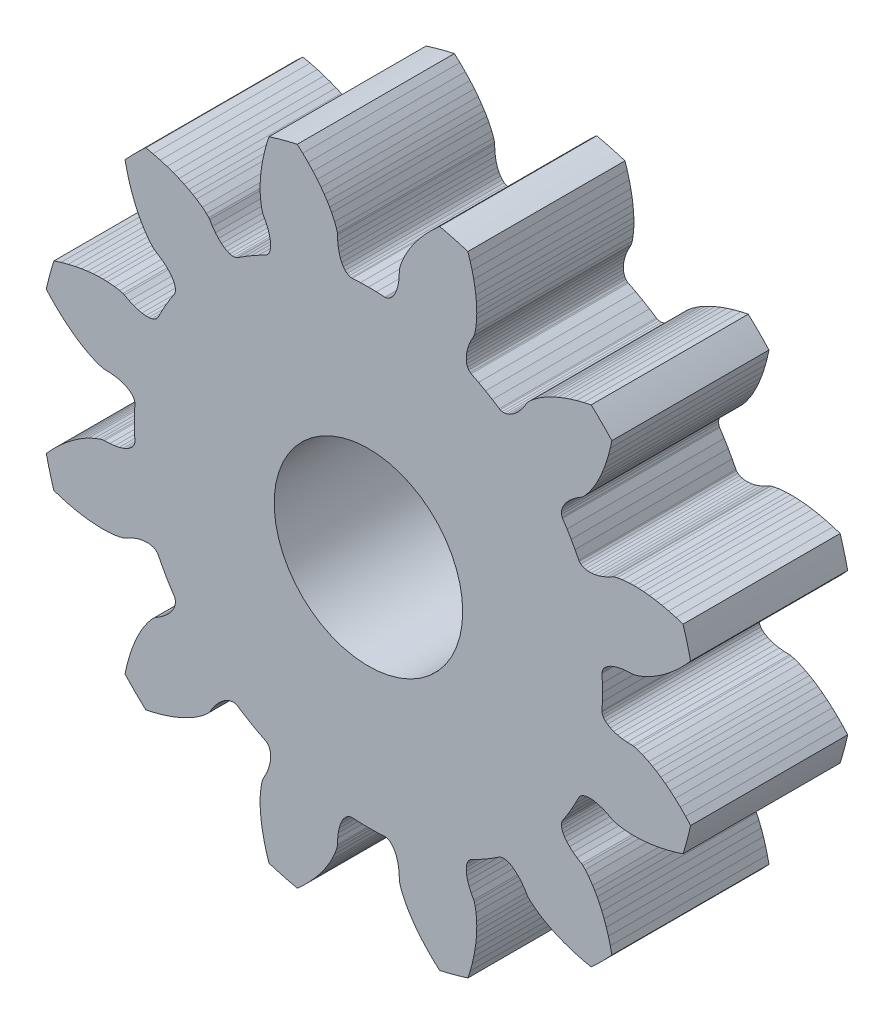
SolidWorks part; units mm, degrees
ref_plane "Płaszczyzna przednia" through (0, 0, 0) normal (0, 0, 1) x (1, 0, 0)
ref_plane "Płaszczyzna górna" through (0, 0, 0) normal (0, 1, 0) x (1, 0, 0)
ref_plane "Płaszczyzna prawa" through (0, 0, 0) normal (1, 0, 0) x (0, 0, -1)
sketch "szkic" plane through (0, 0, 0) normal (0, 0, 1) x (1, 0, 0)
  line L0 (13.3041, -6.8561) -> (13.3646, -6.6243)
  line L1 (13.3646, -6.6243) -> (13.4305, -6.4094)
  line L2 (13.4305, -6.4094) -> (13.5003, -6.2115)
  line L3 (13.5003, -6.2115) -> (13.5727, -6.0307)
  line L4 (13.5727, -6.0307) -> (13.6464, -5.8671)
  line L5 (13.6464, -5.8671) -> (13.7211, -5.718)
  line L6 (13.7211, -5.718) -> (13.7935, -5.5877)
  line L7 (13.7935, -5.5877) -> (13.8642, -5.472)
  line L8 (13.8642, -5.472) -> (13.9934, -5.2871)
  line L9 (13.9934, -5.2871) -> (14.1006, -5.158)
  line L10 (14.1006, -5.158) -> (14.1765, -5.0806)
  line L11 (14.1765, -5.0806) -> (14.2153, -5.0522)
  line L12 (14.2153, -5.0522) -> (14.3621, -4.9616)
  line L13 (14.3621, -4.9616) -> (14.4896, -4.8682)
  line L14 (14.4896, -4.8682) -> (14.5978, -4.7734)
  line L15 (14.5978, -4.7734) -> (14.6868, -4.6788)
  line L16 (14.6868, -4.6788) -> (14.7569, -4.5857)
  line L17 (14.7569, -4.5857) -> (14.8083, -4.4956)
  line L18 (14.8083, -4.4956) -> (14.8415, -4.4098)
  line L19 (14.8415, -4.4098) -> (14.8569, -4.3297)
  line L20 (14.8569, -4.3297) -> (14.8551, -4.2567)
  line L21 (14.8551, -4.2567) -> (14.8367, -4.192)
  line L22 (14.8367, -4.192) -> (14.8215, -4.1631)
  line L23 (14.8215, -4.1631) -> (14.6788, -3.9428)
  line L24 (14.6788, -3.9428) -> (14.5481, -3.725)
  line L25 (14.5481, -3.725) -> (14.4249, -3.5029)
  line L26 (14.4249, -3.5029) -> (14.3054, -3.2691)
  line L27 (14.3054, -3.2691) -> (14.288, -3.2416)
  line L28 (14.288, -3.2416) -> (14.2411, -3.1933)
  line L29 (14.2411, -3.1933) -> (14.1788, -3.1552)
  line L30 (14.1788, -3.1552) -> (14.1017, -3.1285)
  line L31 (14.1017, -3.1285) -> (14.0109, -3.1144)
  line L32 (14.0109, -3.1144) -> (13.9071, -3.1138)
  line L33 (13.9071, -3.1138) -> (13.7915, -3.128)
  line L34 (13.7915, -3.128) -> (13.665, -3.1577)
  line L35 (13.665, -3.1577) -> (13.5289, -3.2041)
  line L36 (13.5289, -3.2041) -> (13.3842, -3.2678)
  line L37 (13.3842, -3.2678) -> (13.2323, -3.3497)
  line L38 (13.2323, -3.3497) -> (13.1884, -3.369)
  line L39 (13.1884, -3.369) -> (13.0833, -3.3961)
  line L40 (13.0833, -3.3961) -> (12.918, -3.4244)
  line L41 (12.918, -3.4244) -> (12.6932, -3.4438)
  line L42 (12.6932, -3.4438) -> (12.5577, -3.4472)
  line L43 (12.5577, -3.4472) -> (12.4086, -3.4447)
  line L44 (12.4086, -3.4447) -> (12.2421, -3.4349)
  line L45 (12.2421, -3.4349) -> (12.0636, -3.4169)
  line L46 (12.0636, -3.4169) -> (11.8708, -3.3892)
  line L47 (11.8708, -3.3892) -> (11.6645, -3.3507)
  line L48 (11.6645, -3.3507) -> (11.4455, -3.3003)
  line L49 (11.4455, -3.3003) -> (11.2145, -3.2368)
  line L50 (11.2145, -3.2368) -> (10.9882, -3.1643)
  line L51 (10.7474, -2.2655) -> (10.9071, -2.0896)
  line L52 (10.9071, -2.0896) -> (11.0754, -1.9191)
  line L53 (11.0754, -1.9191) -> (11.2399, -1.7659)
  line L54 (11.2399, -1.7659) -> (11.3993, -1.6295)
  line L55 (11.3993, -1.6295) -> (11.5524, -1.5091)
  line L56 (11.5524, -1.5091) -> (11.698, -1.4042)
  line L57 (11.698, -1.4042) -> (11.8373, -1.3125)
  line L58 (11.8373, -1.3125) -> (11.9651, -1.2358)
  line L59 (11.9651, -1.2358) -> (12.0842, -1.171)
  line L60 (12.0842, -1.171) -> (12.2886, -1.0754)
  line L61 (12.2886, -1.0754) -> (12.4459, -1.0172)
  line L62 (12.4459, -1.0172) -> (12.5504, -0.9882)
  line L63 (12.5504, -0.9882) -> (12.5981, -0.983)
  line L64 (12.5981, -0.983) -> (12.7706, -0.9779)
  line L65 (12.7706, -0.9779) -> (12.9278, -0.9608)
  line L66 (12.9278, -0.9608) -> (13.0688, -0.9328)
  line L67 (13.0688, -0.9328) -> (13.1933, -0.8953)
  line L68 (13.1933, -0.8953) -> (13.3005, -0.8498)
  line L69 (13.3005, -0.8498) -> (13.3901, -0.7974)
  line L70 (13.3901, -0.7974) -> (13.4617, -0.7397)
  line L71 (13.4617, -0.7397) -> (13.515, -0.6781)
  line L72 (13.515, -0.6781) -> (13.55, -0.6139)
  line L73 (13.55, -0.6139) -> (13.5665, -0.5487)
  line L74 (13.5665, -0.5487) -> (13.5677, -0.5161)
  line L75 (13.5677, -0.5161) -> (13.5543, -0.2539)
  line L76 (13.5543, -0.2539) -> (13.55, 0)
  line L77 (13.55, 0) -> (13.5543, 0.2539)
  line L78 (13.5543, 0.2539) -> (13.5677, 0.5161)
  line L79 (13.5677, 0.5161) -> (13.5665, 0.5487)
  line L80 (13.5665, 0.5487) -> (13.55, 0.6139)
  line L81 (13.55, 0.6139) -> (13.515, 0.6781)
  line L82 (13.515, 0.6781) -> (13.4617, 0.7397)
  line L83 (13.4617, 0.7397) -> (13.3901, 0.7974)
  line L84 (13.3901, 0.7974) -> (13.3005, 0.8498)
  line L85 (13.3005, 0.8498) -> (13.1933, 0.8953)
  line L86 (13.1933, 0.8953) -> (13.0688, 0.9328)
  line L87 (13.0688, 0.9328) -> (12.9278, 0.9608)
  line L88 (12.9278, 0.9608) -> (12.7706, 0.9779)
  line L89 (12.7706, 0.9779) -> (12.5981, 0.983)
  line L90 (12.5981, 0.983) -> (12.5504, 0.9882)
  line L91 (12.5504, 0.9882) -> (12.4459, 1.0172)
  line L92 (12.4459, 1.0172) -> (12.2886, 1.0754)
  line L93 (12.2886, 1.0754) -> (12.0842, 1.171)
  line L94 (12.0842, 1.171) -> (11.9651, 1.2358)
  line L95 (11.9651, 1.2358) -> (11.8373, 1.3125)
  line L96 (11.8373, 1.3125) -> (11.698, 1.4042)
  line L97 (11.698, 1.4042) -> (11.5524, 1.5091)
  line L98 (11.5524, 1.5091) -> (11.3993, 1.6295)
  line L99 (11.3993, 1.6295) -> (11.2399, 1.7659)
  line L100 (11.2399, 1.7659) -> (11.0754, 1.9191)
  line L101 (11.0754, 1.9191) -> (10.9071, 2.0896)
  line L102 (10.9071, 2.0896) -> (10.7474, 2.2655)
  line L103 (10.9882, 3.1643) -> (11.2145, 3.2368)
  line L104 (11.2145, 3.2368) -> (11.4455, 3.3003)
  line L105 (11.4455, 3.3003) -> (11.6645, 3.3507)
  line L106 (11.6645, 3.3507) -> (11.8708, 3.3892)
  line L107 (11.8708, 3.3892) -> (12.0636, 3.4169)
  line L108 (12.0636, 3.4169) -> (12.2421, 3.4349)
  line L109 (12.2421, 3.4349) -> (12.4086, 3.4447)
  line L110 (12.4086, 3.4447) -> (12.5577, 3.4472)
  line L111 (12.5577, 3.4472) -> (12.6932, 3.4438)
  line L112 (12.6932, 3.4438) -> (12.918, 3.4244)
  line L113 (12.918, 3.4244) -> (13.0833, 3.3961)
  line L114 (13.0833, 3.3961) -> (13.1884, 3.369)
  line L115 (13.1884, 3.369) -> (13.2323, 3.3497)
  line L116 (13.2323, 3.3497) -> (13.3842, 3.2678)
  line L117 (13.3842, 3.2678) -> (13.5289, 3.2041)
  line L118 (13.5289, 3.2041) -> (13.665, 3.1577)
  line L119 (13.665, 3.1577) -> (13.7915, 3.128)
  line L120 (13.7915, 3.128) -> (13.9071, 3.1138)
  line L121 (13.9071, 3.1138) -> (14.0109, 3.1144)
  line L122 (14.0109, 3.1144) -> (14.1017, 3.1285)
  line L123 (14.1017, 3.1285) -> (14.1788, 3.1552)
  line L124 (14.1788, 3.1552) -> (14.2411, 3.1933)
  line L125 (14.2411, 3.1933) -> (14.288, 3.2416)
  line L126 (14.288, 3.2416) -> (14.3054, 3.2691)
  line L127 (14.3054, 3.2691) -> (14.4249, 3.5029)
  line L128 (14.4249, 3.5029) -> (14.5481, 3.725)
  line L129 (14.5481, 3.725) -> (14.6788, 3.9428)
  line L130 (14.6788, 3.9428) -> (14.8215, 4.1631)
  line L131 (14.8215, 4.1631) -> (14.8367, 4.192)
  line L132 (14.8367, 4.192) -> (14.8551, 4.2567)
  line L133 (14.8551, 4.2567) -> (14.8569, 4.3297)
  line L134 (14.8569, 4.3297) -> (14.8415, 4.4098)
  line L135 (14.8415, 4.4098) -> (14.8083, 4.4956)
  line L136 (14.8083, 4.4956) -> (14.7569, 4.5857)
  line L137 (14.7569, 4.5857) -> (14.6868, 4.6788)
  line L138 (14.6868, 4.6788) -> (14.5978, 4.7734)
  line L139 (14.5978, 4.7734) -> (14.4896, 4.8682)
  line L140 (14.4896, 4.8682) -> (14.3621, 4.9616)
  line L141 (14.3621, 4.9616) -> (14.2153, 5.0522)
  line L142 (14.2153, 5.0522) -> (14.1765, 5.0806)
  line L143 (14.1765, 5.0806) -> (14.1006, 5.158)
  line L144 (14.1006, 5.158) -> (13.9934, 5.2871)
  line L145 (13.9934, 5.2871) -> (13.8642, 5.472)
  line L146 (13.8642, 5.472) -> (13.7935, 5.5877)
  line L147 (13.7935, 5.5877) -> (13.7211, 5.718)
  line L148 (13.7211, 5.718) -> (13.6464, 5.8671)
  line L149 (13.6464, 5.8671) -> (13.5727, 6.0307)
  line L150 (13.5727, 6.0307) -> (13.5003, 6.2115)
  line L151 (13.5003, 6.2115) -> (13.4305, 6.4094)
  line L152 (13.4305, 6.4094) -> (13.3646, 6.6243)
  line L153 (13.3646, 6.6243) -> (13.3041, 6.8561)
  line L154 (13.3041, 6.8561) -> (13.2537, 7.0883)
  line L155 (13.9117, 7.7463) -> (14.1439, 7.6959)
  line L156 (14.1439, 7.6959) -> (14.3757, 7.6354)
  line L157 (14.3757, 7.6354) -> (14.5906, 7.5695)
  line L158 (14.5906, 7.5695) -> (14.7885, 7.4997)
  line L159 (14.7885, 7.4997) -> (14.9693, 7.4273)
  line L160 (14.9693, 7.4273) -> (15.1329, 7.3536)
  line L161 (15.1329, 7.3536) -> (15.282, 7.2789)
  line L162 (15.282, 7.2789) -> (15.4123, 7.2065)
  line L163 (15.4123, 7.2065) -> (15.528, 7.1358)
  line L164 (15.528, 7.1358) -> (15.7129, 7.0066)
  line L165 (15.7129, 7.0066) -> (15.842, 6.8994)
  line L166 (15.842, 6.8994) -> (15.9194, 6.8235)
  line L167 (15.9194, 6.8235) -> (15.9478, 6.7847)
  line L168 (15.9478, 6.7847) -> (16.0384, 6.6379)
  line L169 (16.0384, 6.6379) -> (16.1318, 6.5104)
  line L170 (16.1318, 6.5104) -> (16.2266, 6.4022)
  line L171 (16.2266, 6.4022) -> (16.3212, 6.3132)
  line L172 (16.3212, 6.3132) -> (16.4143, 6.2431)
  line L173 (16.4143, 6.2431) -> (16.5044, 6.1917)
  line L174 (16.5044, 6.1917) -> (16.5902, 6.1585)
  line L175 (16.5902, 6.1585) -> (16.6703, 6.1431)
  line L176 (16.6703, 6.1431) -> (16.7433, 6.1449)
  line L177 (16.7433, 6.1449) -> (16.808, 6.1633)
  line L178 (16.808, 6.1633) -> (16.8369, 6.1785)
  line L179 (16.8369, 6.1785) -> (17.0572, 6.3212)
  line L180 (17.0572, 6.3212) -> (17.275, 6.4519)
  line L181 (17.275, 6.4519) -> (17.4971, 6.5751)
  line L182 (17.4971, 6.5751) -> (17.7309, 6.6946)
  line L183 (17.7309, 6.6946) -> (17.7584, 6.712)
  line L184 (17.7584, 6.712) -> (17.8067, 6.7589)
  line L185 (17.8067, 6.7589) -> (17.8448, 6.8212)
  line L186 (17.8448, 6.8212) -> (17.8715, 6.8983)
  line L187 (17.8715, 6.8983) -> (17.8856, 6.9891)
  line L188 (17.8856, 6.9891) -> (17.8862, 7.0929)
  line L189 (17.8862, 7.0929) -> (17.872, 7.2085)
  line L190 (17.872, 7.2085) -> (17.8423, 7.335)
  line L191 (17.8423, 7.335) -> (17.7959, 7.4711)
  line L192 (17.7959, 7.4711) -> (17.7322, 7.6158)
  line L193 (17.7322, 7.6158) -> (17.6503, 7.7677)
  line L194 (17.6503, 7.7677) -> (17.631, 7.8116)
  line L195 (17.631, 7.8116) -> (17.6039, 7.9167)
  line L196 (17.6039, 7.9167) -> (17.5756, 8.082)
  line L197 (17.5756, 8.082) -> (17.5562, 8.3068)
  line L198 (17.5562, 8.3068) -> (17.5528, 8.4423)
  line L199 (17.5528, 8.4423) -> (17.5553, 8.5914)
  line L200 (17.5553, 8.5914) -> (17.5651, 8.7579)
  line L201 (17.5651, 8.7579) -> (17.5831, 8.9364)
  line L202 (17.5831, 8.9364) -> (17.6108, 9.1292)
  line L203 (17.6108, 9.1292) -> (17.6493, 9.3355)
  line L204 (17.6493, 9.3355) -> (17.6997, 9.5545)
  line L205 (17.6997, 9.5545) -> (17.7632, 9.7855)
  line L206 (17.7632, 9.7855) -> (17.8357, 10.0118)
  line L207 (18.7345, 10.2526) -> (18.9104, 10.0929)
  line L208 (18.9104, 10.0929) -> (19.0809, 9.9246)
  line L209 (19.0809, 9.9246) -> (19.2341, 9.7601)
  line L210 (19.2341, 9.7601) -> (19.3706, 9.6007)
  line L211 (19.3706, 9.6007) -> (19.4909, 9.4476)
  line L212 (19.4909, 9.4476) -> (19.5958, 9.302)
  line L213 (19.5958, 9.302) -> (19.6875, 9.1627)
  line L214 (19.6875, 9.1627) -> (19.7642, 9.0349)
  line L215 (19.7642, 9.0349) -> (19.829, 8.9158)
  line L216 (19.829, 8.9158) -> (19.9246, 8.7114)
  line L217 (19.9246, 8.7114) -> (19.9828, 8.5541)
  line L218 (19.9828, 8.5541) -> (20.0118, 8.4496)
  line L219 (20.0118, 8.4496) -> (20.017, 8.4019)
  line L220 (20.017, 8.4019) -> (20.0221, 8.2294)
  line L221 (20.0221, 8.2294) -> (20.0392, 8.0722)
  line L222 (20.0392, 8.0722) -> (20.0672, 7.9311)
  line L223 (20.0672, 7.9311) -> (20.1046, 7.8068)
  line L224 (20.1046, 7.8068) -> (20.1502, 7.6995)
  line L225 (20.1502, 7.6995) -> (20.2026, 7.61)
  line L226 (20.2026, 7.61) -> (20.2603, 7.5383)
  line L227 (20.2603, 7.5383) -> (20.3219, 7.485)
  line L228 (20.3219, 7.485) -> (20.3861, 7.45)
  line L229 (20.3861, 7.45) -> (20.4513, 7.4335)
  line L230 (20.4513, 7.4335) -> (20.4839, 7.4323)
  line L231 (20.4839, 7.4323) -> (20.7461, 7.4457)
  line L232 (20.7461, 7.4457) -> (21, 7.45)
  line L233 (21, 7.45) -> (21.2539, 7.4457)
  line L234 (21.2539, 7.4457) -> (21.5161, 7.4323)
  line L235 (21.5161, 7.4323) -> (21.5487, 7.4335)
  line L236 (21.5487, 7.4335) -> (21.6139, 7.45)
  line L237 (21.6139, 7.45) -> (21.6781, 7.485)
  line L238 (21.6781, 7.485) -> (21.7397, 7.5383)
  line L239 (21.7397, 7.5383) -> (21.7974, 7.61)
  line L240 (21.7974, 7.61) -> (21.8498, 7.6995)
  line L241 (21.8498, 7.6995) -> (21.8954, 7.8068)
  line L242 (21.8954, 7.8068) -> (21.9328, 7.9311)
  line L243 (21.9328, 7.9311) -> (21.9608, 8.0722)
  line L244 (21.9608, 8.0722) -> (21.9779, 8.2294)
  line L245 (21.9779, 8.2294) -> (21.983, 8.4019)
  line L246 (21.983, 8.4019) -> (21.9882, 8.4496)
  line L247 (21.9882, 8.4496) -> (22.0172, 8.5541)
  line L248 (22.0172, 8.5541) -> (22.0754, 8.7114)
  line L249 (22.0754, 8.7114) -> (22.171, 8.9158)
  line L250 (22.171, 8.9158) -> (22.2358, 9.0349)
  line L251 (22.2358, 9.0349) -> (22.3125, 9.1627)
  line L252 (22.3125, 9.1627) -> (22.4042, 9.302)
  line L253 (22.4042, 9.302) -> (22.5091, 9.4476)
  line L254 (22.5091, 9.4476) -> (22.6294, 9.6007)
  line L255 (22.6294, 9.6007) -> (22.7659, 9.7601)
  line L256 (22.7659, 9.7601) -> (22.9191, 9.9246)
  line L257 (22.9191, 9.9246) -> (23.0896, 10.0929)
  line L258 (23.0896, 10.0929) -> (23.2655, 10.2526)
  line L259 (24.1643, 10.0118) -> (24.2368, 9.7855)
  line L260 (24.2368, 9.7855) -> (24.3003, 9.5545)
  line L261 (24.3003, 9.5545) -> (24.3507, 9.3355)
  line L262 (24.3507, 9.3355) -> (24.3892, 9.1292)
  line L263 (24.3892, 9.1292) -> (24.4169, 8.9364)
  line L264 (24.4169, 8.9364) -> (24.4349, 8.7579)
  line L265 (24.4349, 8.7579) -> (24.4447, 8.5914)
  line L266 (24.4447, 8.5914) -> (24.4472, 8.4423)
  line L267 (24.4472, 8.4423) -> (24.4438, 8.3068)
  line L268 (24.4438, 8.3068) -> (24.4244, 8.082)
  line L269 (24.4244, 8.082) -> (24.3961, 7.9167)
  line L270 (24.3961, 7.9167) -> (24.369, 7.8116)
  line L271 (24.369, 7.8116) -> (24.3497, 7.7677)
  line L272 (24.3497, 7.7677) -> (24.2678, 7.6158)
  line L273 (24.2678, 7.6158) -> (24.2041, 7.4711)
  line L274 (24.2041, 7.4711) -> (24.1577, 7.335)
  line L275 (24.1577, 7.335) -> (24.128, 7.2085)
  line L276 (24.128, 7.2085) -> (24.1138, 7.0929)
  line L277 (24.1138, 7.0929) -> (24.1144, 6.9891)
  line L278 (24.1144, 6.9891) -> (24.1285, 6.8983)
  line L279 (24.1285, 6.8983) -> (24.1552, 6.8212)
  line L280 (24.1552, 6.8212) -> (24.1933, 6.7589)
  line L281 (24.1933, 6.7589) -> (24.2416, 6.712)
  line L282 (24.2416, 6.712) -> (24.2691, 6.6946)
  line L283 (24.2691, 6.6946) -> (24.5029, 6.5751)
  line L284 (24.5029, 6.5751) -> (24.725, 6.4519)
  line L285 (24.725, 6.4519) -> (24.9428, 6.3212)
  line L286 (24.9428, 6.3212) -> (25.1631, 6.1785)
  line L287 (25.1631, 6.1785) -> (25.192, 6.1633)
  line L288 (25.192, 6.1633) -> (25.2567, 6.1449)
  line L289 (25.2567, 6.1449) -> (25.3297, 6.1431)
  line L290 (25.3297, 6.1431) -> (25.4098, 6.1585)
  line L291 (25.4098, 6.1585) -> (25.4956, 6.1917)
  line L292 (25.4956, 6.1917) -> (25.5857, 6.2431)
  line L293 (25.5857, 6.2431) -> (25.6788, 6.3132)
  line L294 (25.6788, 6.3132) -> (25.7734, 6.4022)
  line L295 (25.7734, 6.4022) -> (25.8682, 6.5104)
  line L296 (25.8682, 6.5104) -> (25.9616, 6.6379)
  line L297 (25.9616, 6.6379) -> (26.0522, 6.7847)
  line L298 (26.0522, 6.7847) -> (26.0806, 6.8235)
  line L299 (26.0806, 6.8235) -> (26.158, 6.8994)
  line L300 (26.158, 6.8994) -> (26.2871, 7.0066)
  line L301 (26.2871, 7.0066) -> (26.472, 7.1358)
  line L302 (26.472, 7.1358) -> (26.5877, 7.2065)
  line L303 (26.5877, 7.2065) -> (26.718, 7.2789)
  line L304 (26.718, 7.2789) -> (26.8671, 7.3536)
  line L305 (26.8671, 7.3536) -> (27.0307, 7.4273)
  line L306 (27.0307, 7.4273) -> (27.2115, 7.4997)
  line L307 (27.2115, 7.4997) -> (27.4094, 7.5695)
  line L308 (27.4094, 7.5695) -> (27.6243, 7.6354)
  line L309 (27.6243, 7.6354) -> (27.8561, 7.6959)
  line L310 (27.8561, 7.6959) -> (28.0883, 7.7463)
  line L311 (28.7463, 7.0883) -> (28.6959, 6.8561)
  line L312 (28.6959, 6.8561) -> (28.6354, 6.6243)
  line L313 (28.6354, 6.6243) -> (28.5695, 6.4094)
  line L314 (28.5695, 6.4094) -> (28.4997, 6.2115)
  line L315 (28.4997, 6.2115) -> (28.4273, 6.0307)
  line L316 (28.4273, 6.0307) -> (28.3536, 5.8671)
  line L317 (28.3536, 5.8671) -> (28.2789, 5.718)
  line L318 (28.2789, 5.718) -> (28.2065, 5.5877)
  line L319 (28.2065, 5.5877) -> (28.1358, 5.472)
  line L320 (28.1358, 5.472) -> (28.0066, 5.2871)
  line L321 (28.0066, 5.2871) -> (27.8994, 5.158)
  line L322 (27.8994, 5.158) -> (27.8235, 5.0806)
  line L323 (27.8235, 5.0806) -> (27.7847, 5.0522)
  line L324 (27.7847, 5.0522) -> (27.6379, 4.9616)
  line L325 (27.6379, 4.9616) -> (27.5104, 4.8682)
  line L326 (27.5104, 4.8682) -> (27.4022, 4.7734)
  line L327 (27.4022, 4.7734) -> (27.3132, 4.6788)
  line L328 (27.3132, 4.6788) -> (27.2431, 4.5857)
  line L329 (27.2431, 4.5857) -> (27.1917, 4.4956)
  line L330 (27.1917, 4.4956) -> (27.1585, 4.4098)
  line L331 (27.1585, 4.4098) -> (27.1431, 4.3297)
  line L332 (27.1431, 4.3297) -> (27.1449, 4.2567)
  line L333 (27.1449, 4.2567) -> (27.1633, 4.192)
  line L334 (27.1633, 4.192) -> (27.1785, 4.1631)
  line L335 (27.1785, 4.1631) -> (27.3212, 3.9428)
  line L336 (27.3212, 3.9428) -> (27.4519, 3.725)
  line L337 (27.4519, 3.725) -> (27.5751, 3.5029)
  line L338 (27.5751, 3.5029) -> (27.6946, 3.2691)
  line L339 (27.6946, 3.2691) -> (27.712, 3.2416)
  line L340 (27.712, 3.2416) -> (27.7589, 3.1933)
  line L341 (27.7589, 3.1933) -> (27.8212, 3.1552)
  line L342 (27.8212, 3.1552) -> (27.8983, 3.1285)
  line L343 (27.8983, 3.1285) -> (27.9891, 3.1144)
  line L344 (27.9891, 3.1144) -> (28.0929, 3.1138)
  line L345 (28.0929, 3.1138) -> (28.2085, 3.128)
  line L346 (28.2085, 3.128) -> (28.335, 3.1577)
  line L347 (28.335, 3.1577) -> (28.4711, 3.2041)
  line L348 (28.4711, 3.2041) -> (28.6158, 3.2678)
  line L349 (28.6158, 3.2678) -> (28.7677, 3.3497)
  line L350 (28.7677, 3.3497) -> (28.8116, 3.369)
  line L351 (28.8116, 3.369) -> (28.9167, 3.3961)
  line L352 (28.9167, 3.3961) -> (29.082, 3.4244)
  line L353 (29.082, 3.4244) -> (29.3068, 3.4438)
  line L354 (29.3068, 3.4438) -> (29.4423, 3.4472)
  line L355 (29.4423, 3.4472) -> (29.5914, 3.4447)
  line L356 (29.5914, 3.4447) -> (29.7579, 3.4349)
  line L357 (29.7579, 3.4349) -> (29.9364, 3.4169)
  line L358 (29.9364, 3.4169) -> (30.1292, 3.3892)
  line L359 (30.1292, 3.3892) -> (30.3355, 3.3507)
  line L360 (30.3355, 3.3507) -> (30.5545, 3.3003)
  line L361 (30.5545, 3.3003) -> (30.7855, 3.2368)
  line L362 (30.7855, 3.2368) -> (31.0118, 3.1643)
  line L363 (31.2526, 2.2655) -> (31.0929, 2.0896)
  line L364 (31.0929, 2.0896) -> (30.9246, 1.9191)
  line L365 (30.9246, 1.9191) -> (30.7601, 1.7659)
  line L366 (30.7601, 1.7659) -> (30.6007, 1.6295)
  line L367 (30.6007, 1.6295) -> (30.4476, 1.5091)
  line L368 (30.4476, 1.5091) -> (30.302, 1.4042)
  line L369 (30.302, 1.4042) -> (30.1627, 1.3125)
  line L370 (30.1627, 1.3125) -> (30.0349, 1.2358)
  line L371 (30.0349, 1.2358) -> (29.9158, 1.171)
  line L372 (29.9158, 1.171) -> (29.7114, 1.0754)
  line L373 (29.7114, 1.0754) -> (29.5541, 1.0172)
  line L374 (29.5541, 1.0172) -> (29.4496, 0.9882)
  line L375 (29.4496, 0.9882) -> (29.4019, 0.983)
  line L376 (29.4019, 0.983) -> (29.2294, 0.9779)
  line L377 (29.2294, 0.9779) -> (29.0722, 0.9608)
  line L378 (29.0722, 0.9608) -> (28.9311, 0.9328)
  line L379 (28.9311, 0.9328) -> (28.8068, 0.8953)
  line L380 (28.8068, 0.8953) -> (28.6995, 0.8498)
  line L381 (28.6995, 0.8498) -> (28.61, 0.7974)
  line L382 (28.61, 0.7974) -> (28.5383, 0.7397)
  line L383 (28.5383, 0.7397) -> (28.485, 0.6781)
  line L384 (28.485, 0.6781) -> (28.45, 0.6139)
  line L385 (28.45, 0.6139) -> (28.4335, 0.5487)
  line L386 (28.4335, 0.5487) -> (28.4323, 0.5161)
  line L387 (28.4323, 0.5161) -> (28.4457, 0.2539)
  line L388 (28.4457, 0.2539) -> (28.45, 0)
  line L389 (28.45, 0) -> (28.4457, -0.2539)
  line L390 (28.4457, -0.2539) -> (28.4323, -0.5161)
  line L391 (28.4323, -0.5161) -> (28.4335, -0.5487)
  line L392 (28.4335, -0.5487) -> (28.45, -0.6139)
  line L393 (28.45, -0.6139) -> (28.485, -0.6781)
  line L394 (28.485, -0.6781) -> (28.5383, -0.7397)
  line L395 (28.5383, -0.7397) -> (28.61, -0.7974)
  line L396 (28.61, -0.7974) -> (28.6995, -0.8498)
  line L397 (28.6995, -0.8498) -> (28.8068, -0.8953)
  line L398 (28.8068, -0.8953) -> (28.9311, -0.9328)
  line L399 (28.9311, -0.9328) -> (29.0722, -0.9608)
  line L400 (29.0722, -0.9608) -> (29.2294, -0.9779)
  line L401 (29.2294, -0.9779) -> (29.4019, -0.983)
  line L402 (29.4019, -0.983) -> (29.4496, -0.9882)
  line L403 (29.4496, -0.9882) -> (29.5541, -1.0172)
  line L404 (29.5541, -1.0172) -> (29.7114, -1.0754)
  line L405 (29.7114, -1.0754) -> (29.9158, -1.171)
  line L406 (29.9158, -1.171) -> (30.0349, -1.2358)
  line L407 (30.0349, -1.2358) -> (30.1627, -1.3125)
  line L408 (30.1627, -1.3125) -> (30.302, -1.4042)
  line L409 (30.302, -1.4042) -> (30.4476, -1.5091)
  line L410 (30.4476, -1.5091) -> (30.6007, -1.6295)
  line L411 (30.6007, -1.6295) -> (30.7601, -1.7659)
  line L412 (30.7601, -1.7659) -> (30.9246, -1.9191)
  line L413 (30.9246, -1.9191) -> (31.0929, -2.0896)
  line L414 (31.0929, -2.0896) -> (31.2526, -2.2655)
  line L415 (31.0118, -3.1643) -> (30.7855, -3.2368)
  line L416 (30.7855, -3.2368) -> (30.5545, -3.3003)
  line L417 (30.5545, -3.3003) -> (30.3355, -3.3507)
  line L418 (30.3355, -3.3507) -> (30.1292, -3.3892)
  line L419 (30.1292, -3.3892) -> (29.9364, -3.4169)
  line L420 (29.9364, -3.4169) -> (29.7579, -3.4349)
  line L421 (29.7579, -3.4349) -> (29.5914, -3.4447)
  line L422 (29.5914, -3.4447) -> (29.4423, -3.4472)
  line L423 (29.4423, -3.4472) -> (29.3068, -3.4438)
  line L424 (29.3068, -3.4438) -> (29.082, -3.4244)
  line L425 (29.082, -3.4244) -> (28.9167, -3.3961)
  line L426 (28.9167, -3.3961) -> (28.8116, -3.369)
  line L427 (28.8116, -3.369) -> (28.7677, -3.3497)
  line L428 (28.7677, -3.3497) -> (28.6158, -3.2678)
  line L429 (28.6158, -3.2678) -> (28.4711, -3.2041)
  line L430 (28.4711, -3.2041) -> (28.335, -3.1577)
  line L431 (28.335, -3.1577) -> (28.2085, -3.128)
  line L432 (28.2085, -3.128) -> (28.0929, -3.1138)
  line L433 (28.0929, -3.1138) -> (27.9891, -3.1144)
  line L434 (27.9891, -3.1144) -> (27.8983, -3.1285)
  line L435 (27.8983, -3.1285) -> (27.8212, -3.1552)
  line L436 (27.8212, -3.1552) -> (27.7589, -3.1933)
  line L437 (27.7589, -3.1933) -> (27.712, -3.2416)
  line L438 (27.712, -3.2416) -> (27.6946, -3.2691)
  line L439 (27.6946, -3.2691) -> (27.5751, -3.5029)
  line L440 (27.5751, -3.5029) -> (27.4519, -3.725)
  line L441 (27.4519, -3.725) -> (27.3212, -3.9428)
  line L442 (27.3212, -3.9428) -> (27.1785, -4.1631)
  line L443 (27.1785, -4.1631) -> (27.1633, -4.192)
  line L444 (27.1633, -4.192) -> (27.1449, -4.2567)
  line L445 (27.1449, -4.2567) -> (27.1431, -4.3297)
  line L446 (27.1431, -4.3297) -> (27.1585, -4.4098)
  line L447 (27.1585, -4.4098) -> (27.1917, -4.4956)
  line L448 (27.1917, -4.4956) -> (27.2431, -4.5857)
  line L449 (27.2431, -4.5857) -> (27.3132, -4.6788)
  line L450 (27.3132, -4.6788) -> (27.4022, -4.7734)
  line L451 (27.4022, -4.7734) -> (27.5104, -4.8682)
  line L452 (27.5104, -4.8682) -> (27.6379, -4.9616)
  line L453 (27.6379, -4.9616) -> (27.7847, -5.0522)
  line L454 (27.7847, -5.0522) -> (27.8235, -5.0806)
  line L455 (27.8235, -5.0806) -> (27.8994, -5.158)
  line L456 (27.8994, -5.158) -> (28.0066, -5.2871)
  line L457 (28.0066, -5.2871) -> (28.1358, -5.472)
  line L458 (28.1358, -5.472) -> (28.2065, -5.5877)
  line L459 (28.2065, -5.5877) -> (28.2789, -5.718)
  line L460 (28.2789, -5.718) -> (28.3536, -5.8671)
  line L461 (28.3536, -5.8671) -> (28.4273, -6.0307)
  line L462 (28.4273, -6.0307) -> (28.4997, -6.2115)
  line L463 (28.4997, -6.2115) -> (28.5695, -6.4094)
  line L464 (28.5695, -6.4094) -> (28.6354, -6.6243)
  line L465 (28.6354, -6.6243) -> (28.6959, -6.8561)
  line L466 (28.6959, -6.8561) -> (28.7463, -7.0883)
  line L467 (28.0883, -7.7463) -> (27.8561, -7.6959)
  line L468 (27.8561, -7.6959) -> (27.6243, -7.6354)
  line L469 (27.6243, -7.6354) -> (27.4094, -7.5695)
  line L470 (27.4094, -7.5695) -> (27.2115, -7.4997)
  line L471 (27.2115, -7.4997) -> (27.0307, -7.4273)
  line L472 (27.0307, -7.4273) -> (26.8671, -7.3536)
  line L473 (26.8671, -7.3536) -> (26.718, -7.2789)
  line L474 (26.718, -7.2789) -> (26.5877, -7.2065)
  line L475 (26.5877, -7.2065) -> (26.472, -7.1358)
  line L476 (26.472, -7.1358) -> (26.2871, -7.0066)
  line L477 (26.2871, -7.0066) -> (26.158, -6.8994)
  line L478 (26.158, -6.8994) -> (26.0806, -6.8235)
  line L479 (26.0806, -6.8235) -> (26.0522, -6.7847)
  line L480 (26.0522, -6.7847) -> (25.9616, -6.6379)
  line L481 (25.9616, -6.6379) -> (25.8682, -6.5104)
  line L482 (25.8682, -6.5104) -> (25.7734, -6.4022)
  line L483 (25.7734, -6.4022) -> (25.6788, -6.3132)
  line L484 (25.6788, -6.3132) -> (25.5857, -6.2431)
  line L485 (25.5857, -6.2431) -> (25.4956, -6.1917)
  line L486 (25.4956, -6.1917) -> (25.4098, -6.1585)
  line L487 (25.4098, -6.1585) -> (25.3297, -6.1431)
  line L488 (25.3297, -6.1431) -> (25.2567, -6.1449)
  line L489 (25.2567, -6.1449) -> (25.192, -6.1633)
  line L490 (25.192, -6.1633) -> (25.1631, -6.1785)
  line L491 (25.1631, -6.1785) -> (24.9428, -6.3212)
  line L492 (24.9428, -6.3212) -> (24.725, -6.4519)
  line L493 (24.725, -6.4519) -> (24.5029, -6.5751)
  line L494 (24.5029, -6.5751) -> (24.2691, -6.6946)
  line L495 (24.2691, -6.6946) -> (24.2416, -6.712)
  line L496 (24.2416, -6.712) -> (24.1933, -6.7589)
  line L497 (24.1933, -6.7589) -> (24.1552, -6.8212)
  line L498 (24.1552, -6.8212) -> (24.1285, -6.8983)
  line L499 (24.1285, -6.8983) -> (24.1144, -6.9891)
  line L500 (24.1144, -6.9891) -> (24.1138, -7.0929)
  line L501 (24.1138, -7.0929) -> (24.128, -7.2085)
  line L502 (24.128, -7.2085) -> (24.1577, -7.335)
  line L503 (24.1577, -7.335) -> (24.2041, -7.4711)
  line L504 (24.2041, -7.4711) -> (24.2678, -7.6158)
  line L505 (24.2678, -7.6158) -> (24.3497, -7.7677)
  line L506 (24.3497, -7.7677) -> (24.369, -7.8116)
  line L507 (24.369, -7.8116) -> (24.3961, -7.9167)
  line L508 (24.3961, -7.9167) -> (24.4244, -8.082)
  line L509 (24.4244, -8.082) -> (24.4438, -8.3068)
  line L510 (24.4438, -8.3068) -> (24.4472, -8.4423)
  line L511 (24.4472, -8.4423) -> (24.4447, -8.5914)
  line L512 (24.4447, -8.5914) -> (24.4349, -8.7579)
  line L513 (24.4349, -8.7579) -> (24.4169, -8.9364)
  line L514 (24.4169, -8.9364) -> (24.3892, -9.1292)
  line L515 (24.3892, -9.1292) -> (24.3507, -9.3355)
  line L516 (24.3507, -9.3355) -> (24.3003, -9.5545)
  line L517 (24.3003, -9.5545) -> (24.2368, -9.7855)
  line L518 (24.2368, -9.7855) -> (24.1643, -10.0118)
  line L519 (23.2655, -10.2526) -> (23.0896, -10.0929)
  line L520 (23.0896, -10.0929) -> (22.9191, -9.9246)
  line L521 (22.9191, -9.9246) -> (22.7659, -9.7601)
  line L522 (22.7659, -9.7601) -> (22.6294, -9.6007)
  line L523 (22.6294, -9.6007) -> (22.5091, -9.4476)
  line L524 (22.5091, -9.4476) -> (22.4042, -9.302)
  line L525 (22.4042, -9.302) -> (22.3125, -9.1627)
  line L526 (22.3125, -9.1627) -> (22.2358, -9.0349)
  line L527 (22.2358, -9.0349) -> (22.171, -8.9158)
  line L528 (22.171, -8.9158) -> (22.0754, -8.7114)
  line L529 (22.0754, -8.7114) -> (22.0172, -8.5541)
  line L530 (22.0172, -8.5541) -> (21.9882, -8.4496)
  line L531 (21.9882, -8.4496) -> (21.983, -8.4019)
  line L532 (21.983, -8.4019) -> (21.9779, -8.2294)
  line L533 (21.9779, -8.2294) -> (21.9608, -8.0722)
  line L534 (21.9608, -8.0722) -> (21.9328, -7.9311)
  line L535 (21.9328, -7.9311) -> (21.8954, -7.8068)
  line L536 (21.8954, -7.8068) -> (21.8498, -7.6995)
  line L537 (21.8498, -7.6995) -> (21.7974, -7.61)
  line L538 (21.7974, -7.61) -> (21.7397, -7.5383)
  line L539 (21.7397, -7.5383) -> (21.6781, -7.485)
  line L540 (21.6781, -7.485) -> (21.6139, -7.45)
  line L541 (21.6139, -7.45) -> (21.5487, -7.4335)
  line L542 (21.5487, -7.4335) -> (21.5161, -7.4323)
  line L543 (21.5161, -7.4323) -> (21.2539, -7.4457)
  line L544 (21.2539, -7.4457) -> (21, -7.45)
  line L545 (21, -7.45) -> (20.7461, -7.4457)
  line L546 (20.7461, -7.4457) -> (20.4839, -7.4323)
  line L547 (20.4839, -7.4323) -> (20.4513, -7.4335)
  line L548 (20.4513, -7.4335) -> (20.3861, -7.45)
  line L549 (20.3861, -7.45) -> (20.3219, -7.485)
  line L550 (20.3219, -7.485) -> (20.2603, -7.5383)
  line L551 (20.2603, -7.5383) -> (20.2026, -7.61)
  line L552 (20.2026, -7.61) -> (20.1502, -7.6995)
  line L553 (20.1502, -7.6995) -> (20.1046, -7.8068)
  line L554 (20.1046, -7.8068) -> (20.0672, -7.9311)
  line L555 (20.0672, -7.9311) -> (20.0392, -8.0722)
  line L556 (20.0392, -8.0722) -> (20.0221, -8.2294)
  line L557 (20.0221, -8.2294) -> (20.017, -8.4019)
  line L558 (20.017, -8.4019) -> (20.0118, -8.4496)
  line L559 (20.0118, -8.4496) -> (19.9828, -8.5541)
  line L560 (19.9828, -8.5541) -> (19.9246, -8.7114)
  line L561 (19.9246, -8.7114) -> (19.829, -8.9158)
  line L562 (19.829, -8.9158) -> (19.7642, -9.0349)
  line L563 (19.7642, -9.0349) -> (19.6875, -9.1627)
  line L564 (19.6875, -9.1627) -> (19.5958, -9.302)
  line L565 (19.5958, -9.302) -> (19.4909, -9.4476)
  line L566 (19.4909, -9.4476) -> (19.3706, -9.6007)
  line L567 (19.3706, -9.6007) -> (19.2341, -9.7601)
  line L568 (19.2341, -9.7601) -> (19.0809, -9.9246)
  line L569 (19.0809, -9.9246) -> (18.9104, -10.0929)
  line L570 (18.9104, -10.0929) -> (18.7345, -10.2526)
  line L571 (17.8357, -10.0118) -> (17.7632, -9.7855)
  line L572 (17.7632, -9.7855) -> (17.6997, -9.5545)
  line L573 (17.6997, -9.5545) -> (17.6493, -9.3355)
  line L574 (17.6493, -9.3355) -> (17.6108, -9.1292)
  line L575 (17.6108, -9.1292) -> (17.5831, -8.9364)
  line L576 (17.5831, -8.9364) -> (17.5651, -8.7579)
  line L577 (17.5651, -8.7579) -> (17.5553, -8.5914)
  line L578 (17.5553, -8.5914) -> (17.5528, -8.4423)
  line L579 (17.5528, -8.4423) -> (17.5562, -8.3068)
  line L580 (17.5562, -8.3068) -> (17.5756, -8.082)
  line L581 (17.5756, -8.082) -> (17.6039, -7.9167)
  line L582 (17.6039, -7.9167) -> (17.631, -7.8116)
  line L583 (17.631, -7.8116) -> (17.6503, -7.7677)
  line L584 (17.6503, -7.7677) -> (17.7322, -7.6158)
  line L585 (17.7322, -7.6158) -> (17.7959, -7.4711)
  line L586 (17.7959, -7.4711) -> (17.8423, -7.335)
  line L587 (17.8423, -7.335) -> (17.872, -7.2085)
  line L588 (17.872, -7.2085) -> (17.8862, -7.0929)
  line L589 (17.8862, -7.0929) -> (17.8856, -6.9891)
  line L590 (17.8856, -6.9891) -> (17.8715, -6.8983)
  line L591 (17.8715, -6.8983) -> (17.8448, -6.8212)
  line L592 (17.8448, -6.8212) -> (17.8067, -6.7589)
  line L593 (17.8067, -6.7589) -> (17.7584, -6.712)
  line L594 (17.7584, -6.712) -> (17.7309, -6.6946)
  line L595 (17.7309, -6.6946) -> (17.4971, -6.5751)
  line L596 (17.4971, -6.5751) -> (17.275, -6.4519)
  line L597 (17.275, -6.4519) -> (17.0572, -6.3212)
  line L598 (17.0572, -6.3212) -> (16.8369, -6.1785)
  line L599 (16.8369, -6.1785) -> (16.808, -6.1633)
  line L600 (16.808, -6.1633) -> (16.7433, -6.1449)
  line L601 (16.7433, -6.1449) -> (16.6703, -6.1431)
  line L602 (16.6703, -6.1431) -> (16.5902, -6.1585)
  line L603 (16.5902, -6.1585) -> (16.5044, -6.1917)
  line L604 (16.5044, -6.1917) -> (16.4143, -6.2431)
  line L605 (16.4143, -6.2431) -> (16.3212, -6.3132)
  line L606 (16.3212, -6.3132) -> (16.2266, -6.4022)
  line L607 (16.2266, -6.4022) -> (16.1318, -6.5104)
  line L608 (16.1318, -6.5104) -> (16.0384, -6.6379)
  line L609 (16.0384, -6.6379) -> (15.9478, -6.7847)
  line L610 (15.9478, -6.7847) -> (15.9194, -6.8235)
  line L611 (15.9194, -6.8235) -> (15.842, -6.8994)
  line L612 (15.842, -6.8994) -> (15.7129, -7.0066)
  line L613 (15.7129, -7.0066) -> (15.528, -7.1358)
  line L614 (15.528, -7.1358) -> (15.4123, -7.2065)
  line L615 (15.4123, -7.2065) -> (15.282, -7.2789)
  line L616 (15.282, -7.2789) -> (15.1329, -7.3536)
  line L617 (15.1329, -7.3536) -> (14.9693, -7.4273)
  line L618 (14.9693, -7.4273) -> (14.7885, -7.4997)
  line L619 (14.7885, -7.4997) -> (14.5906, -7.5695)
  line L620 (14.5906, -7.5695) -> (14.3757, -7.6354)
  line L621 (14.3757, -7.6354) -> (14.1439, -7.6959)
  line L622 (14.1439, -7.6959) -> (13.9117, -7.7463)
  line L623 (13.2537, -7.0883) -> (13.3041, -6.8561)
  circle A0 centre (21, 0) radius 3
  arc A2 (10.7474, -2.2655) -> (10.9882, -3.1643) centre (21, 0) ccw
  arc A3 (10.9882, 3.1643) -> (10.7474, 2.2655) centre (21, 0) ccw
  arc A4 (13.9117, 7.7463) -> (13.2537, 7.0883) centre (21, 0) ccw
  arc A5 (18.7345, 10.2526) -> (17.8357, 10.0118) centre (21, 0) ccw
  arc A6 (24.1643, 10.0118) -> (23.2655, 10.2526) centre (21, 0) ccw
  arc A7 (28.7463, 7.0883) -> (28.0883, 7.7463) centre (21, 0) ccw
  arc A8 (31.2526, 2.2655) -> (31.0118, 3.1643) centre (21, 0) ccw
  arc A9 (31.0118, -3.1643) -> (31.2526, -2.2655) centre (21, 0) ccw
  arc A10 (28.0883, -7.7463) -> (28.7463, -7.0883) centre (21, 0) ccw
  arc A11 (23.2655, -10.2526) -> (24.1643, -10.0118) centre (21, 0) ccw
  arc A12 (17.8357, -10.0118) -> (18.7345, -10.2526) centre (21, 0) ccw
  arc A13 (13.2537, -7.0883) -> (13.9117, -7.7463) centre (21, 0) ccw
  dimension "D1" = 6
extrude "Dodanie-wyciągnięcie1" add sketch "szkic" along normal blind 5
